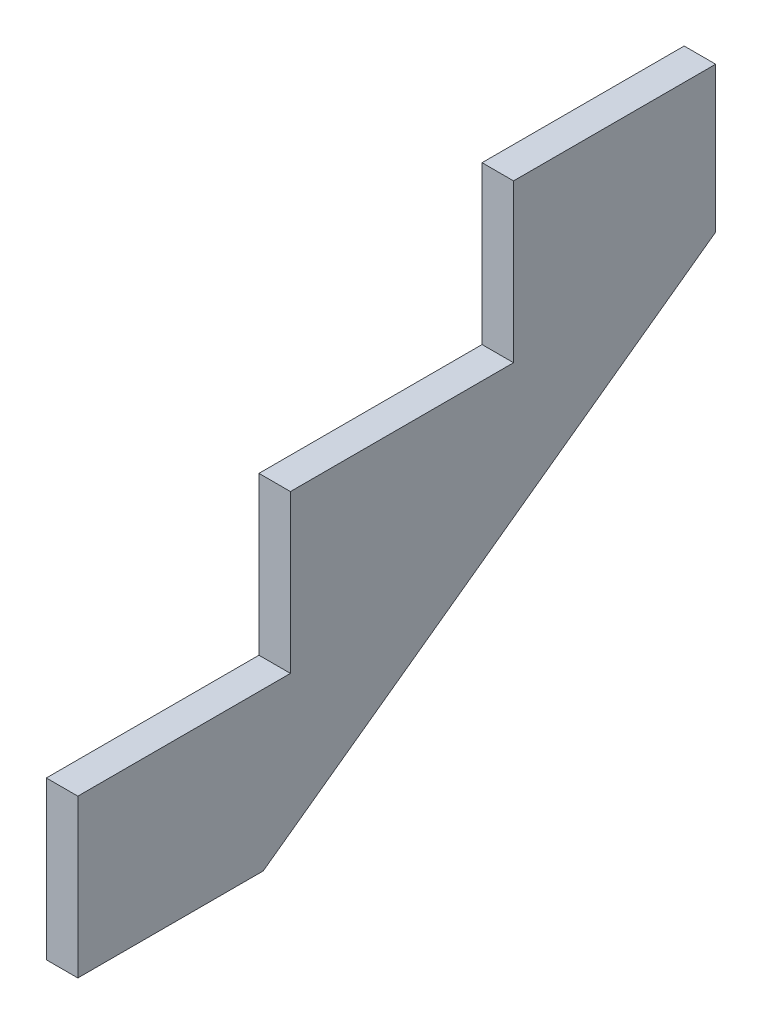
SolidWorks part; units mm, degrees
ref_plane "Front Plane" through (0, 0, 0) normal (0, 0, 1) x (1, 0, 0)
ref_plane "Top Plane" through (0, 0, 0) normal (0, 1, 0) x (1, 0, 0)
ref_plane "Right Plane" through (0, 0, 0) normal (1, 0, 0) x (0, 0, -1)
sketch "Sketch1" plane through (0, 0, 0) normal (1, 0, 0) x (0, 0, -1)
  line L0 (224.2303, 0) -> (771.525, 395.6347)
  line L1 (771.525, 571.5) -> (527.05, 571.5)
  line L6 (0, 0) -> (0, 190.5)
  line L7 (0, 190.5) -> (257.175, 190.5)
  line L10 (257.175, 190.5) -> (257.175, 381)
  line L11 (257.175, 381) -> (527.05, 381)
  line L14 (527.05, 381) -> (527.05, 571.5)
  line L15 (527.05, 571.5) -> (771.525, 571.5)
  line L17 (527.05, 381) -> (498.475, 381)
  line L18 (527.05, 381) -> (527.05, 571.5)
  line L21 (498.475, 381) -> (257.175, 381)
  line L25 (257.175, 190.5) -> (241.3, 190.5)
  line L26 (257.175, 190.5) -> (257.175, 381)
  line L29 (241.3, 190.5) -> (0, 190.5)
  line L34 (0, 0) -> (0, 190.5)
  line L37 (527.05, 571.5) -> (771.525, 571.5)
  line L38 (527.05, 571.5) -> (527.05, 381)
  line L40 (771.525, 571.5) -> (771.525, 395.6347)
  line L41 (0, 0) -> (224.2303, 0)
  line L42 (0, 0) -> (0, 190.5)
  line L43 (0, 190.5) -> (257.175, 190.5)
  dimension "D1" = 244.475
  dimension "D2" = 190.5
  dimension "D3" = 190.5
  dimension "D4" = 257.175
  dimension "D5" = 269.875
  dimension "D6" = 285.75
  dimension "D7" = 175.8653
  dimension "D8" = 571.5
  dimension "D9" = 771.525
  dimension "D10" = 285.75
  dimension "D11" = 131.3647
  dimension "D12" = 135.0848
  dimension "D13" = 224.2303
  dimension "D17" = 190.5
extrude "Boss-Extrude2" add sketch "Sketch1" along normal blind 38.1 contours L6 L41 L0 L40 L1 L14 L11 L10 L7
